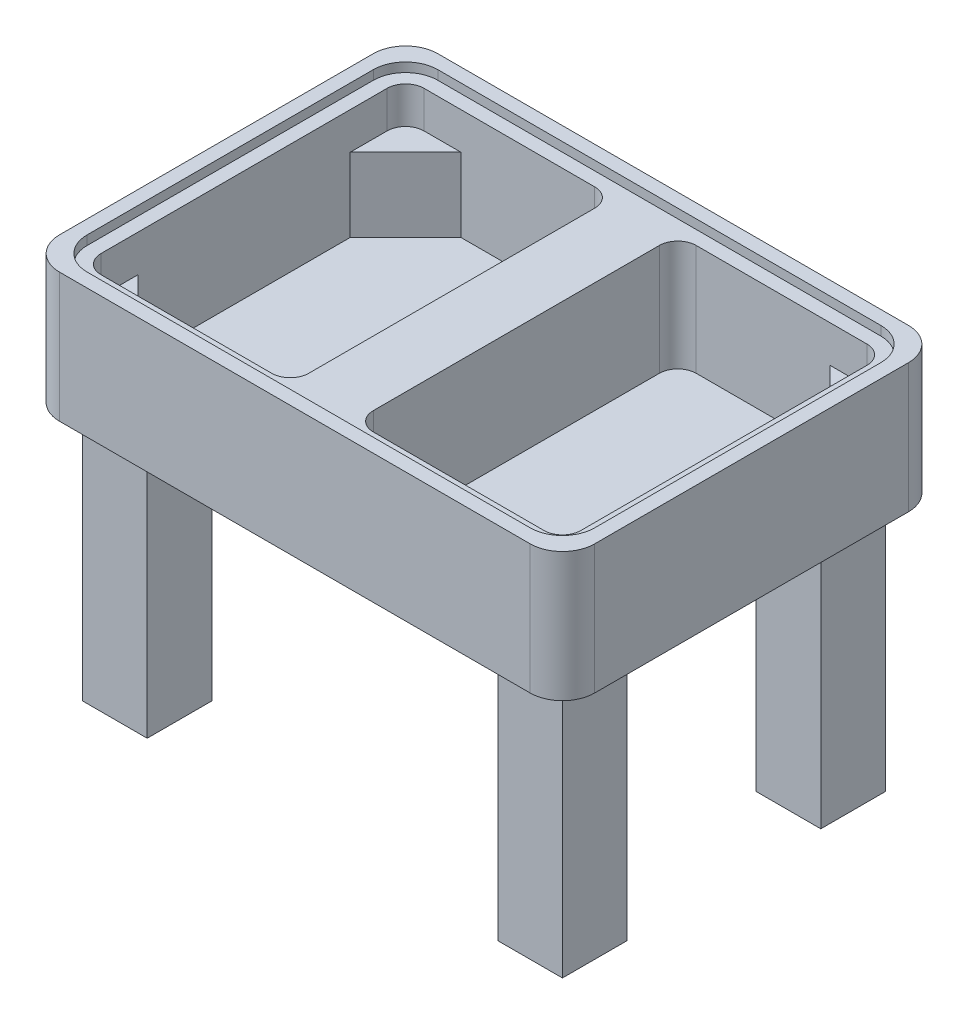
SolidWorks part; units mm, degrees
ref_plane "Front Plane" through (0, 0, 0) normal (0, 0, 1) x (1, 0, 0)
ref_plane "Top Plane" through (0, 0, 0) normal (0, 1, 0) x (1, 0, 0)
ref_plane "Right Plane" through (0, 0, 0) normal (1, 0, 0) x (0, 0, -1)
sketch "Sketch1" plane through (0, 0, 0) normal (0, 1, 0) x (1, 0, 0)
  line L1 (0, 0) -> (580, 0)
  line L2 (0, 0) -> (0, 410)
  line L3 (0, 410) -> (580, 410)
  line L4 (580, 0) -> (580, 410)
  dimension "D1" = 580
  dimension "D2" = 410
extrude "Boss-Extrude1" add sketch "Sketch1" against normal blind 140
sketch "Sketch3" plane through (0, 0, 0) normal (0, 1, 0) x (1, 0, 0)
  line L0 (580, 410) -> (0, 410) construction
  line L1 (15, 395) -> (565, 395)
  line L2 (15, 395) -> (15, 15)
  line L3 (15, 15) -> (565, 15)
  line L4 (565, 395) -> (565, 15)
  line L5 (0, 410) -> (0, 0) construction
  line L6 (0, 0) -> (580, 0) construction
  line L7 (580, 0) -> (580, 410) construction
  dimension "D1" = 15
  dimension "D2" = 15
  dimension "D3" = 15
  dimension "D4" = 15
extrude "Cut-Extrude1" cut sketch "Sketch3" against normal blind 10
sketch "Sketch2" plane through (0, -10, 0) normal (0, 1, 0) x (1, 0, 0)
  line L0 (580, 410) -> (0, 410) construction
  line L1 (30, 380) -> (255, 380)
  line L2 (30, 380) -> (30, 30)
  line L3 (30, 30) -> (255, 30)
  line L4 (255, 380) -> (255, 30)
  line L5 (0, 410) -> (0, 0) construction
  line L6 (0, 0) -> (580, 0) construction
  line L7 (290, 410) -> (290, 0) construction
  line L8 (550, 30) -> (325, 30)
  line L9 (325, 380) -> (325, 30)
  line L10 (550, 380) -> (325, 380)
  line L11 (550, 380) -> (550, 30)
  dimension "D1" = 30
  dimension "D2" = 30
  dimension "D3" = 30
  dimension "D4" = 255
extrude "Cut-Extrude2" cut sketch "Sketch2" against normal blind 40
sketch "Sketch5" plane through (0, -50, 0) normal (0, 1, 0) x (1, 0, 0)
  line L0 (30, 320) -> (90, 380)
  line L1 (30, 380) -> (30, 30) construction
  line L2 (255, 380) -> (30, 380) construction
  line L5 (255, 380) -> (30, 380) construction
  line L6 (255, 380) -> (90, 380)
  line L7 (290, 395) -> (290, 0) construction
  line L8 (565, 395) -> (15, 395) construction
  line L9 (0, 0) -> (580, 0) construction
  line L10 (0, 205) -> (580, 205) construction
  line L11 (0, 410) -> (0, 0) construction
  line L12 (580, 0) -> (580, 410) construction
  line L13 (30, 90) -> (90, 30)
  line L18 (550, 90) -> (490, 30)
  line L21 (550, 320) -> (490, 380)
  line L22 (550, 30) -> (550, 380) construction
  line L23 (325, 30) -> (550, 30) construction
  line L24 (550, 380) -> (325, 380) construction
  line L25 (325, 380) -> (325, 30) construction
  line L26 (255, 30) -> (255, 380) construction
  line L27 (30, 30) -> (255, 30) construction
  line L28 (30, 320) -> (30, 90)
  line L29 (550, 90) -> (550, 320)
  line L30 (325, 30) -> (490, 30)
  line L31 (490, 380) -> (325, 380)
  line L32 (325, 380) -> (325, 30)
  line L33 (255, 30) -> (255, 380)
  line L34 (90, 30) -> (255, 30)
  dimension "D1" = 60
  dimension "D2" = 60
extrude "Cut-Extrude3" cut sketch "Sketch5" against normal blind 80
fillet "Fillet1" radius 35 8 edges at (565, -5, -15) (565, -5, -395) (15, -5, -395) (15, -5, -15) (0, -70, 0) (580, -70, 0) (580, -70, -410) (0, -70, -410)
sketch "Sketch6" plane through (0, -140, 0) normal (0, -1, 0) x (1, 0, 0)
  line L0 (35, 0) -> (545, 0) construction
  line L1 (30, -30) -> (100, -30)
  line L2 (30, -30) -> (30, -100)
  line L3 (30, -100) -> (100, -100)
  line L4 (100, -30) -> (100, -100)
  line L5 (0, -375) -> (0, -35) construction
  line L6 (290, 0) -> (290, -410) construction
  line L7 (545, -410) -> (35, -410) construction
  line L8 (0, -205) -> (580, -205) construction
  line L9 (580, -35) -> (580, -375) construction
  line L10 (550, -100) -> (480, -100)
  line L11 (480, -30) -> (480, -100)
  line L12 (550, -30) -> (480, -30)
  line L13 (550, -30) -> (550, -100)
  line L14 (550, -310) -> (480, -310)
  line L15 (550, -380) -> (550, -310)
  line L16 (550, -380) -> (480, -380)
  line L17 (480, -380) -> (480, -310)
  line L18 (30, -310) -> (100, -310)
  line L19 (100, -380) -> (100, -310)
  line L20 (30, -380) -> (100, -380)
  line L21 (30, -380) -> (30, -310)
  dimension "D1" = 30
  dimension "D2" = 30
  dimension "D3" = 70
  dimension "D4" = 70
extrude "Boss-Extrude2" add sketch "Sketch6" along normal blind 280
fillet "Fillet2" radius 20 8 edges at (30, -30, -380) (325, -70, -380) (255, -70, -380) (30, -30, -30) (255, -70, -30) (325, -70, -30) (550, -30, -30) (550, -30, -380)
